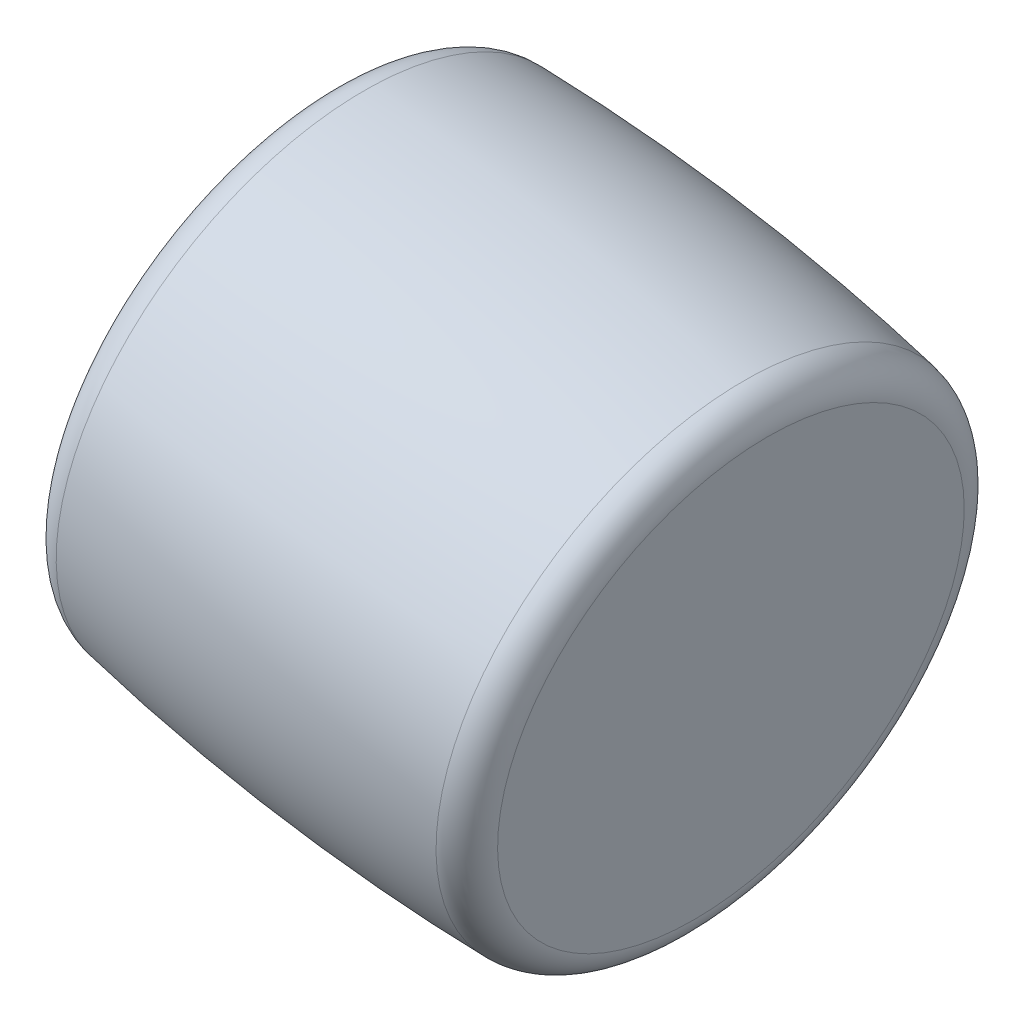
SolidWorks part; units mm, degrees
ref_plane "Front Plane" through (0, 0, 0) normal (0, 0, 1) x (1, 0, 0)
ref_plane "Top Plane" through (0, 0, 0) normal (0, 1, 0) x (1, 0, 0)
ref_plane "Right Plane" through (0, 0, 0) normal (1, 0, 0) x (0, 0, -1)
ref_plane "Plane1" through (0, 0, 0) normal (0, 0, 1) x (1, 0, 0)
sketch "Sketch1" plane through (0, 0, 0) normal (0, 0, 1) x (1, 0, 0)
  line L0 (15.9158, 44.0364) -> (16.7682, 49.3192)
  line L1 (26.9367, 47.6783) -> (26.0842, 42.3956)
  line L2 (26.0842, 42.3956) -> (15.9158, 44.0364)
  line L3 (26.0842, 42.3956) -> (15.9158, 44.0364) construction
  arc A0 (16.7682, 49.3192) -> (17.5608, 49.9479) centre (17.5087, 49.1997) cw
  arc A1 (17.5608, 49.9479) -> (26.3821, 48.5244) centre (14.1154, 0.5519) cw
  arc A2 (26.3821, 48.5244) -> (26.9367, 47.6783) centre (26.1963, 47.7978) cw
revolve "Revolve1" add sketch "Sketch1" angle 360 about L3
